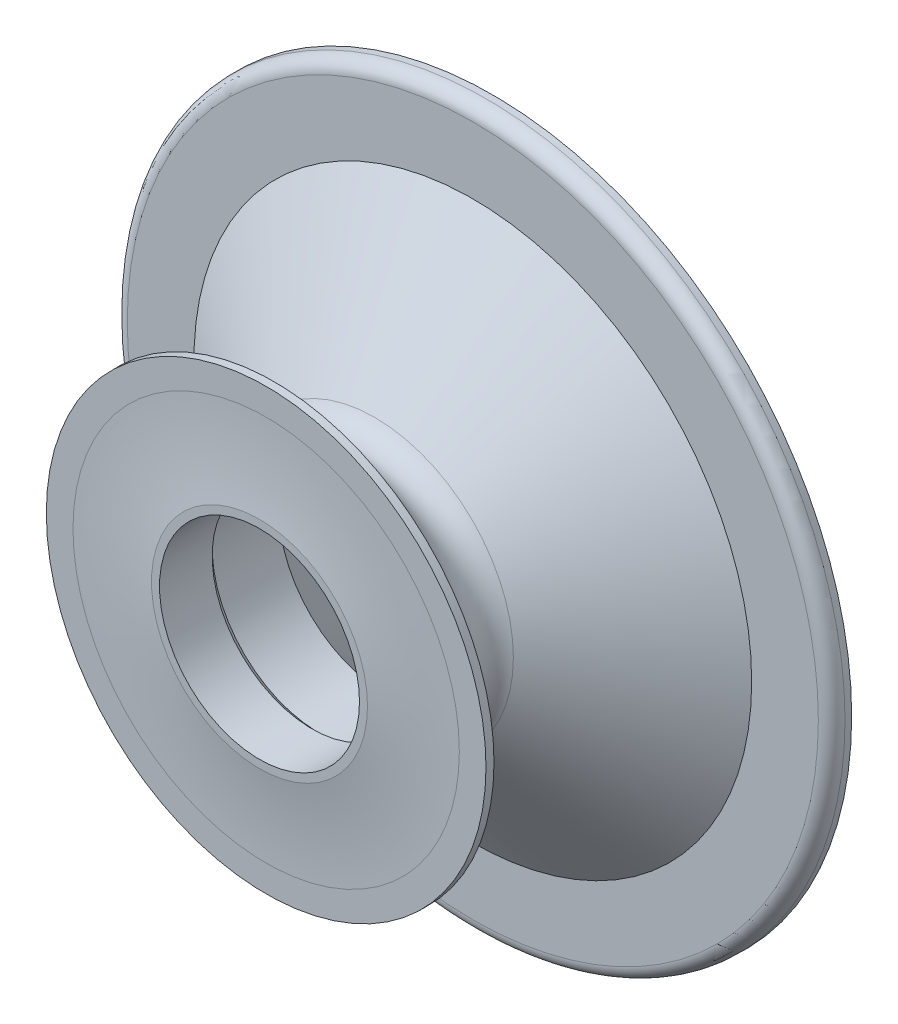
SolidWorks part; units mm, degrees
ref_plane "Front Plane" through (0, 0, 0) normal (0, 0, 1) x (1, 0, 0)
ref_plane "Top Plane" through (0, 0, 0) normal (0, 1, 0) x (1, 0, 0)
ref_plane "Right Plane" through (0, 0, 0) normal (1, 0, 0) x (0, 0, -1)
sketch "Sketch1" plane through (0, 0, 0) normal (1, 0, 0) x (0, 0, -1)
  line L0 (-162.7216, 0) -> (7973.3569, 0) construction
  line L1 (-2.5, 8.05) -> (2.5, 8.05)
  line L2 (10.5, 16.05) -> (2.5, 8.05)
  line L3 (-2.5, 8.05) -> (-3.05, 7.5)
  line L4 (1.6383, 10.4028) -> (9, 20.9164)
  line L5 (-7, 7.5) -> (-3.05, 7.5)
  line L6 (-1.6383, 10.4028) -> (-5.9, 16.4892)
  line L7 (-5.9, 16.4892) -> (-6.5, 16.4892)
  line L8 (-6.5, 16.4892) -> (-6.5, 14.4892)
  line L11 (9, 20.9164) -> (9, 26.9164)
  line L12 (9, 26.9164) -> (10.5, 26.9164)
  line L13 (-7, 7.5) -> (-7, 8.1)
  line L14 (10.5, 26.9164) -> (10.5, 16.05)
  arc A0 (1.6383, 10.4028) -> (-1.6383, 10.4028) centre (0, 11.55) cw
  arc A1 (-6.5, 14.4892) -> (-7, 8.1) centre (-47.5716, 14.4892) cw
  point P5 (0, 9.55)
  point P8 (0, 8.05)
  point P9 (0, 9.55)
  point P17 (0, 14.311)
  dimension "D1" = 45
  dimension "D6" = 15
  dimension "D9" = 2
  dimension "D11" = 2
  dimension "D2" = 5
  dimension "D3" = 16.1
  dimension "D4" = 1.5
  dimension "D5" = 35
  dimension "D7" = 6.5
  dimension "D8" = 0.6
  dimension "D10" = 0.6
  dimension "D12" = 0.5
  dimension "D13" = 9
  dimension "D14" = 6
  dimension "D15" = 1.5
  dimension "D16" = 45
revolve "Revolve1" add sketch "Sketch1" angle 360 about L0
fillet "Fillet1" radius 1 1 edges at (26.9164, 0, -9)
